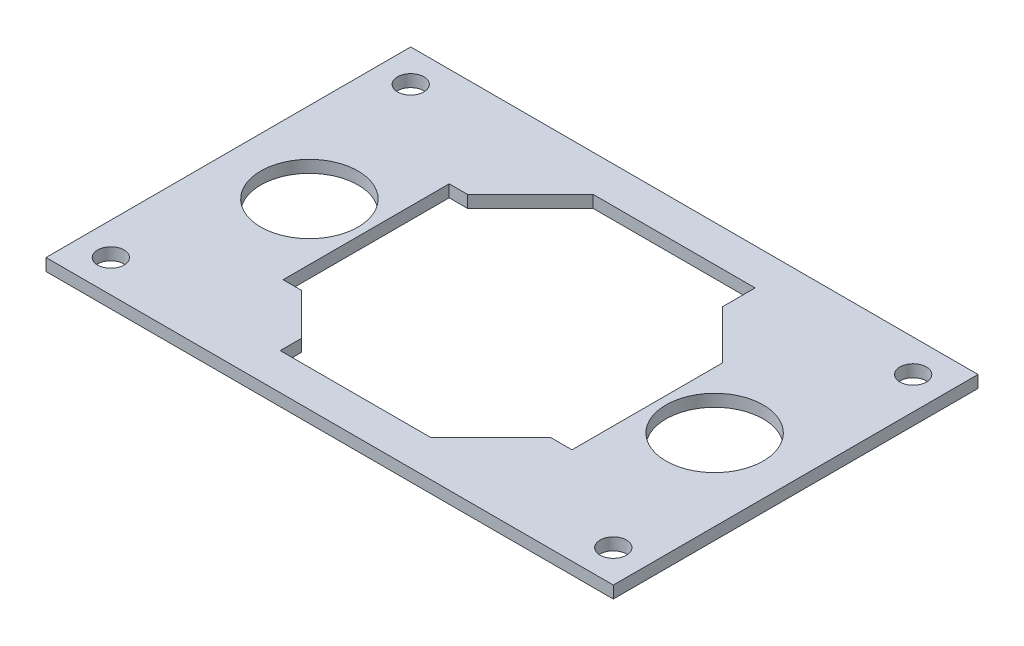
SolidWorks part; units mm, degrees
material "ABS PC"
ref_plane "Front Plane" through (0, 0, 0) normal (0, 0, 1) x (1, 0, 0)
ref_plane "Top Plane" through (0, 0, 0) normal (0, 1, 0) x (1, 0, 0)
ref_plane "Right Plane" through (0, 0, 0) normal (1, 0, 0) x (0, 0, -1)
sketch "Sketch2" plane through (0, 0, 0) normal (0, 1, 0) x (1, 0, 0)
  line L0 (35, 0) -> (0, 0) construction
  line L1 (-35, -22.5) -> (35, -22.5)
  line L2 (-35, -22.5) -> (-35, 22.5)
  line L3 (-35, 22.5) -> (35, 22.5)
  line L4 (35, -22.5) -> (35, 22.5)
  dimension "D1" = 45
  dimension "D2" = 70
  dimension "D3" = 35
extrude "Boss-Extrude1" add sketch "Sketch2" along normal blind 1.5
sketch "Sketch3" plane through (0, 1.5, 0) normal (0, 1, 0) x (1, 0, 0)
  line L0 (-35, 22.5) -> (-35, -22.5) construction
  line L1 (-31, -18.5) -> (31, -18.5) construction
  line L2 (-31, -18.5) -> (-31, 18.5) construction
  line L3 (-31, 18.5) -> (31, 18.5) construction
  line L4 (31, -18.5) -> (31, 18.5) construction
  line L5 (35, 22.5) -> (-35, 22.5) construction
  line L6 (35, -22.5) -> (35, 22.5) construction
  line L7 (-35, -22.5) -> (35, -22.5) construction
  line L8 (-25, 0) -> (25, 0) construction
  circle A0 centre (-31, -18.5) radius 1.625
  circle A1 centre (-31, 18.5) radius 1.625
  circle A2 centre (31, 18.5) radius 1.625
  circle A3 centre (31, -18.5) radius 1.625
  circle A4 centre (-25, 0) radius 6
  circle A5 centre (25, 0) radius 6
  dimension "D5" = 3.25
  dimension "D7" = 12
  dimension "D1" = 4
  dimension "D2" = 4
  dimension "D3" = 4
  dimension "D4" = 4
  dimension "D6" = 50
extrude "Cut-Extrude1" cut sketch "Sketch3" against normal through all
sketch "Sketch4" plane through (0, 1.5, 0) normal (0, 1, 0) x (1, 0, 0)
  line L0 (-10.6, -18) -> (-10.6, -15.4)
  line L1 (-8, 18) -> (12, 18)
  line L2 (-18, 10.25) -> (-18, -10.25)
  line L3 (-10.6, -18) -> (8, -18)
  line L4 (18, 8) -> (18, -10.6)
  line L5 (-10.6, -15.4) -> (-15.75, -10.25)
  line L6 (-15.75, -10.25) -> (-18, -10.25)
  line L7 (-18, 10.25) -> (-15.75, 10.25)
  line L8 (-15.75, 10.25) -> (-8, 18)
  line L9 (12, 18) -> (12, 14)
  line L10 (12, 14) -> (18, 8)
  line L11 (18, -10.6) -> (15.4, -10.6)
  line L12 (15.4, -10.6) -> (8, -18)
  line L13 (-18, 0) -> (0, 0) construction
  line L14 (0, 0) -> (18, 0) construction
  line L15 (0, 0) -> (0, 18) construction
  line L16 (0, 0) -> (0, -18) construction
  dimension "D1" = 45
  dimension "D2" = 10.25
  dimension "D3" = 2.6
  dimension "D4" = 2.6
  dimension "D5" = 4
  dimension "D6" = 10.6
  dimension "D7" = 2.25
  dimension "D8" = 12
  dimension "D9" = 18
extrude "Cut-Extrude2" cut sketch "Sketch4" against normal through all
